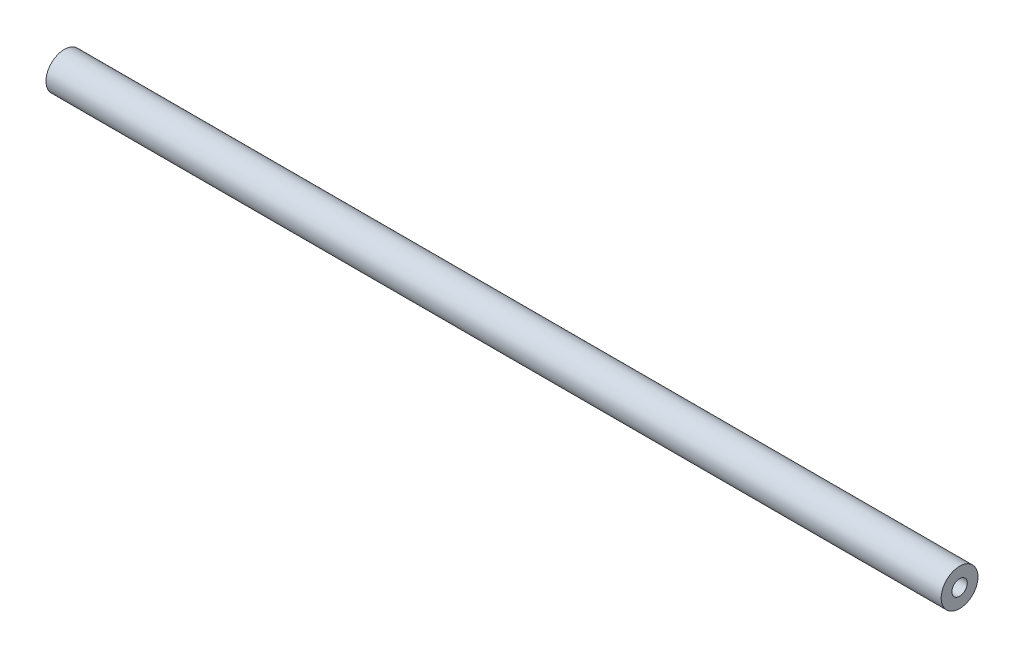
SolidWorks part; units mm, degrees
material "Oak"
ref_plane "Front Plane" through (0, 0, 0) normal (0, 0, 1) x (1, 0, 0)
ref_plane "Top Plane" through (0, 0, 0) normal (0, 1, 0) x (1, 0, 0)
ref_plane "Right Plane" through (0, 0, 0) normal (1, 0, 0) x (0, 0, -1)
sketch "Sketch1" plane through (0, 0, 0) normal (1, 0, 0) x (0, 0, -1)
  circle A0 centre (0, 0) radius 3.9688
  circle A1 centre (0, 0) radius 9.525
  dimension "D1" = 7.9375
  dimension "D2" = 19.05
extrude "Boss-Extrude1" add sketch "Sketch1" along normal mid plane 463.423
